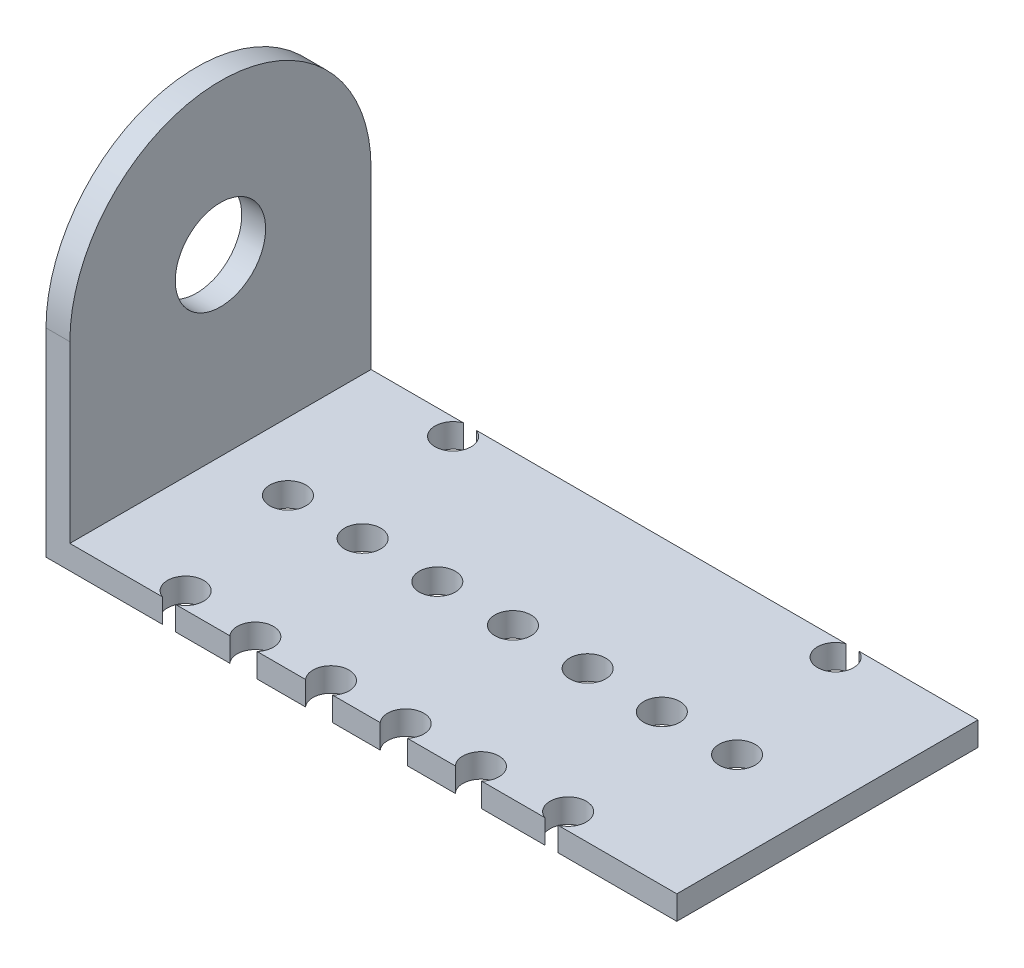
SolidWorks part; units mm, degrees
ref_plane "Front Plane" through (0, 0, 0) normal (0, 0, 1) x (1, 0, 0)
ref_plane "Top Plane" through (0, 0, 0) normal (0, 1, 0) x (1, 0, 0)
ref_plane "Right Plane" through (0, 0, 0) normal (1, 0, 0) x (0, 0, -1)
sketch "Sketch1" plane through (0, 0, 0) normal (0, 1, 0) x (1, 0, 0)
  line L0 (26.18, 0) -> (-26.18, 0) construction
  line L1 (26.18, -12.5) -> (-26.18, -12.5)
  line L2 (26.18, -12.5) -> (26.18, 12.5)
  line L3 (26.18, 12.5) -> (-26.18, 12.5)
  line L4 (-26.18, -12.5) -> (-26.18, 12.5)
  line L5 (26.18, -12.5) -> (-26.18, 12.5) construction
  line L6 (26.18, 12.5) -> (-26.18, -12.5) construction
  line L7 (26.18, 11.4926) -> (-26.18, 11.4926) construction
  line L8 (26.18, -11.4926) -> (-26.18, -11.4926) construction
  line L9 (26.18, -12.5) -> (-26.18, -12.5)
  circle A0 centre (18.68, 0) radius 1.5
  circle A1 centre (12.48, -0.0444) radius 1.5
  circle A2 centre (6.28, 0) radius 1.5
  circle A3 centre (0.08, 0) radius 1.5
  circle A4 centre (-6.2, 0) radius 1.5
  circle A5 centre (-18.6, 0) radius 1.5
  circle A6 centre (-12.4, 0) radius 1.5
  arc A7 (15.2217, 12.5) -> (16.2987, 12.5) centre (15.7602, 11.1) ccw
  circle A12 centre (-15.9898, -11.1) radius 1.5
  arc A13 (-16.5283, 12.5) -> (-15.4513, 12.5) centre (-15.9898, 11.1) ccw
  circle A14 centre (-9.7898, -11.5148) radius 1.5
  circle A15 centre (-3.5098, -11.5148) radius 1.5
  circle A16 centre (2.6902, -11.5148) radius 1.5
  circle A17 centre (8.8902, -11.4704) radius 1.5
  circle A18 centre (15.7602, -11.1) radius 1.5
  point P0 (0, 0)
  dimension "D4" = 3
  dimension "D1" = 52.36
  dimension "D2" = 25
  dimension "D3" = 7.5
  dimension "D5" = 6.2
  dimension "D6" = 6.2
  dimension "D7" = 6.2
  dimension "D8" = 6.2
  dimension "D9" = 6.2
  dimension "D10" = 6.2
  dimension "D11" = 31.75
  dimension "D12" = 22.2
extrude "Boss-Extrude1" add sketch "Sketch1" along normal blind 1.98 contours L1 A18 L2 L3 A7 A13 L4 A12 A14 A15 A16 A17 A6 A5 A4 A3 A2 A1 A0
sketch "Sketch2" plane through (0, 1.98, 0) normal (0, 1, 0) x (1, 0, 0)
  line L0 (-16.5283, -12.5) -> (-26.18, -12.5) construction
  line L1 (-26.18, 12.5) -> (-24.2, 12.5)
  line L2 (-26.18, 12.5) -> (-26.18, -12.5)
  line L3 (-26.18, -12.5) -> (-24.2, -12.5)
  line L4 (-24.2, 12.5) -> (-24.2, -12.5)
  dimension "D1" = 1.98
extrude "Boss-Extrude2" add sketch "Sketch2" along normal blind 14.5
sketch "Sketch3" plane through (-26.18, 0, 0) normal (-1, 0, 0) x (0, 0, 1)
  line L0 (-12.5, 16.48) -> (12.5, 16.48) construction
  circle A0 centre (0, 16.48) radius 12.5
extrude "Boss-Extrude5" add sketch "Sketch3" along direction (-1, 0, 0) on the side against the normal up to surface (1.98 mm away)
sketch "Sketch4" plane through (-26.18, 0, 0) normal (-1, 0, 0) x (0, 0, 1)
  line L0 (-12.5, 16.48) -> (12.5, 16.48) construction
  line L2 (0, 0) -> (0, 27.2673) construction
  arc A0 (12.5, 16.48) -> (-12.5, 16.48) centre (0, 16.48) ccw construction
  circle A1 centre (0, 16.48) radius 3.75
  dimension "D1" = 7.5
extrude "Cut-Extrude1" cut sketch "Sketch4" against normal blind 14.5
